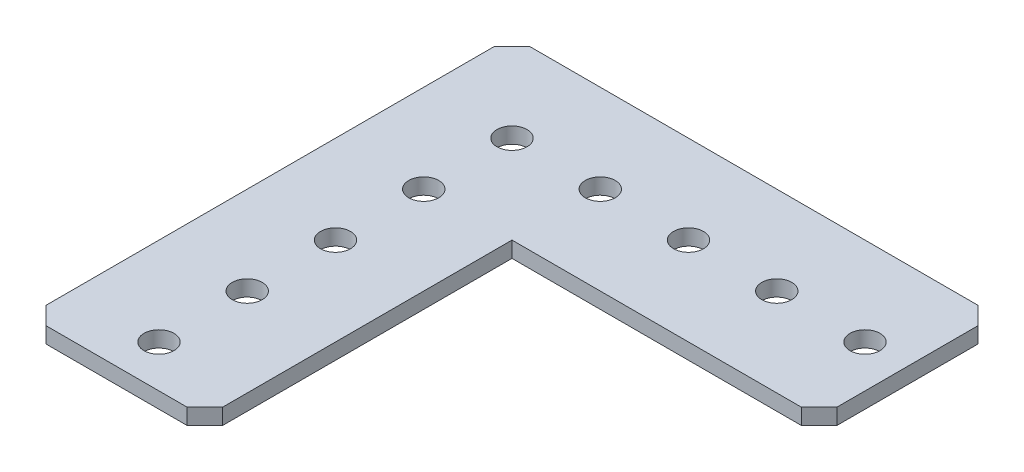
SolidWorks part; units mm, degrees
ref_plane "Front Plane" through (0, 0, 0) normal (0, 0, 1) x (1, 0, 0)
ref_plane "Top Plane" through (0, 0, 0) normal (0, 1, 0) x (1, 0, 0)
ref_plane "Right Plane" through (0, 0, 0) normal (1, 0, 0) x (0, 0, -1)
sketch "Sketch1" plane through (0, 0, 0) normal (0, 1, 0) x (1, 0, 0)
  line L0 (0, 2.54) -> (0, 67.056)
  line L1 (2.54, 69.596) -> (67.056, 69.596)
  line L2 (69.596, 67.056) -> (69.596, 46.736)
  line L3 (67.056, 44.196) -> (25.4, 44.196)
  line L4 (25.4, 44.196) -> (25.4, 2.54)
  line L5 (22.86, 0) -> (2.54, 0)
  line L6 (2.54, 0) -> (0, 2.54)
  line L7 (25.4, 2.54) -> (22.86, 0)
  line L8 (0, 67.056) -> (2.54, 69.596)
  line L9 (67.056, 69.596) -> (69.596, 67.056)
  line L10 (69.596, 46.736) -> (67.056, 44.196)
  line L11 (12.7, 56.896) -> (25.4, 56.896) construction
  line L12 (12.7, 56.896) -> (12.7, 44.196) construction
  circle A0 centre (12.7, 56.896) radius 2.159
  circle A1 centre (25.4, 56.896) radius 2.159
  circle A2 centre (38.1, 56.896) radius 2.159
  circle A3 centre (50.8, 56.896) radius 2.159
  circle A4 centre (63.5, 56.896) radius 2.159
  circle A5 centre (12.7, 44.196) radius 2.159
  circle A6 centre (12.7, 31.496) radius 2.159
  circle A7 centre (12.7, 18.796) radius 2.159
  circle A8 centre (12.7, 6.096) radius 2.159
  point P0 (0, 0)
  point P1 (0, 69.596)
  point P3 (25.4, 0)
  point P4 (69.596, 69.596)
  point P5 (69.596, 44.196)
  dimension "D5" = 4.318
  dimension "D6" = 12.7
  dimension "D1" = 69.596
  dimension "D2" = 69.596
  dimension "D3" = 25.4
  dimension "D4" = 25.4
  dimension "D7" = 12.7
  dimension "D9" = 12.7
  dimension "D11" = 12.7
  dimension "D8" = 5
  dimension "D10" = 5
extrude "Boss-Extrude1" add sketch "Sketch1" along normal blind 2.286
